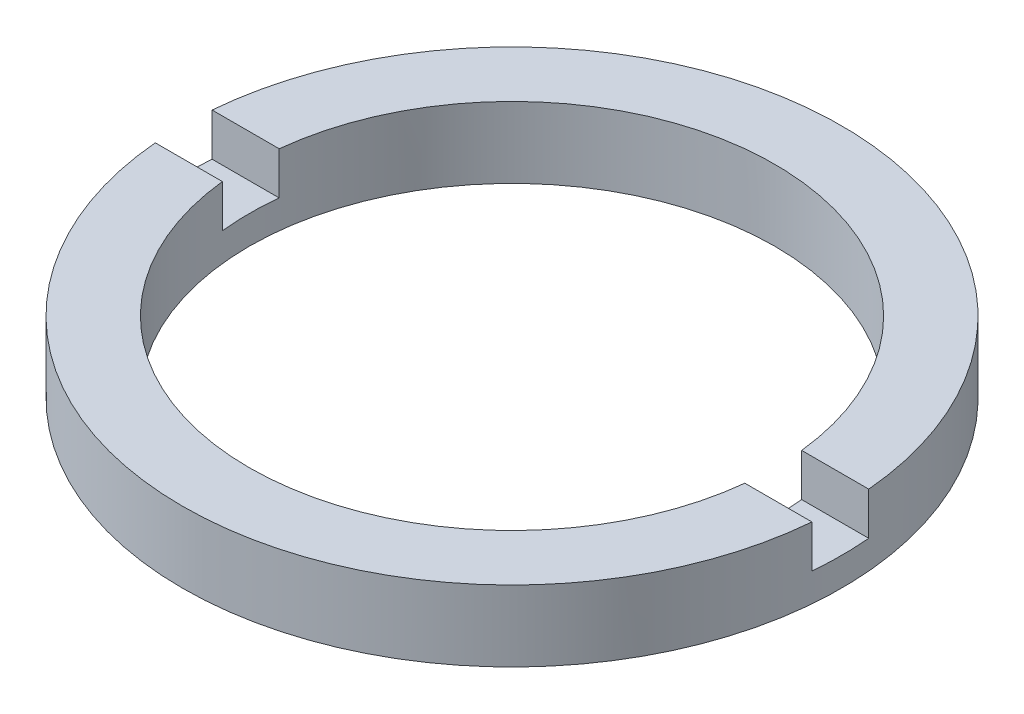
SolidWorks part; units mm, degrees
ref_plane "前视基准面" through (0, 0, 0) normal (0, 0, 1) x (1, 0, 0)
ref_plane "上视基准面" through (0, 0, 0) normal (0, 1, 0) x (1, 0, 0)
ref_plane "右视基准面" through (0, 0, 0) normal (1, 0, 0) x (0, 0, -1)
sketch "草图1" plane through (0, 0, 0) normal (0, 0, 1) x (1, 0, 0)
  line L0 (0, 56.2608) -> (0, -99.1922) construction
  line L1 (9.25, -1.9642) -> (11.6, -1.9642)
  line L4 (11.6, -1.9642) -> (11.6, -4.4642)
  line L5 (9.25, -4.4642) -> (9.25, -1.9642)
  line L7 (9.25, -4.4642) -> (11.6, -4.4642)
  dimension "D1" = 2.5
  dimension "D2" = 11.6
  dimension "D3" = 9.25
revolve "旋转1" add sketch "草图1" angle 360 about L0
cosmetic thread "装饰螺纹线1" parameters "D2"=22.2
sketch "草图2" plane through (0, -1.9642, 0) normal (0, 1, 0) x (1, 0, 0)
  line L0 (-28.67, 0) -> (29.9422, 0) construction
  line L2 (-26.8525, 1) -> (26.8525, 1)
  line L3 (-26.8525, 1) -> (-26.8525, -1)
  line L4 (-26.8525, -1) -> (26.8525, -1)
  line L5 (26.8525, 1) -> (26.8525, -1)
  line L6 (-26.8525, 1) -> (26.8525, -1) construction
  line L7 (-26.8525, -1) -> (26.8525, 1) construction
  point P3 (0, 0)
  dimension "D1" = 2
extrude "切除-拉伸1" cut sketch "草图2" against normal blind 1.5
